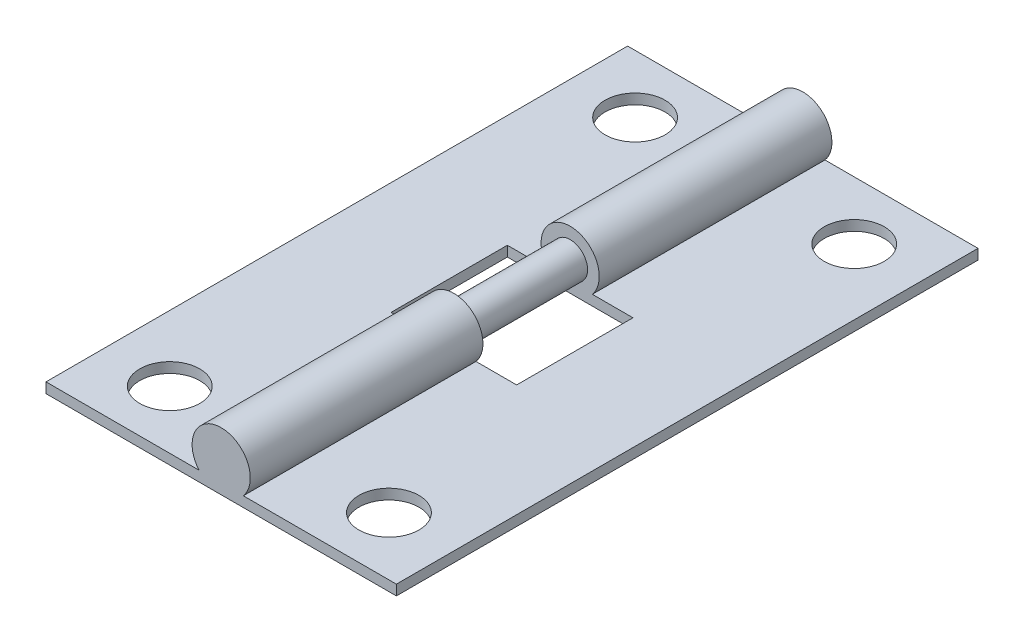
SolidWorks part; units mm, degrees
ref_plane "Front Plane" through (0, 0, 0) normal (0, 0, 1) x (1, 0, 0)
ref_plane "Top Plane" through (0, 0, 0) normal (0, 1, 0) x (1, 0, 0)
ref_plane "Right Plane" through (0, 0, 0) normal (1, 0, 0) x (0, 0, -1)
sketch "Sketch1" plane through (0, 0, 0) normal (0, 0, 1) x (1, 0, 0)
  line L0 (0, 0) -> (19.1262, 0)
  line L1 (19.1262, 0) -> (19.1262, 0.5588)
  line L2 (19.1262, 0.5588) -> (10.7722, 0.5588)
  line L3 (0, 0) -> (0, 0.5588)
  line L4 (0, 0.5588) -> (8.354, 0.5588)
  arc A0 (10.7722, 0.5588) -> (8.354, 0.5588) centre (9.5631, 1.5875) ccw
  dimension "D2" = 3.175
  dimension "D1" = 19.1262
  dimension "D3" = 0.5588
  dimension "D4" = 1.5875
  dimension "D5" = 9.5631
extrude "Boss-Extrude1" add sketch "Sketch1" along normal blind 31.75
sketch "Sketch3" plane through (0, 0, 0) normal (0, -1, 0) x (1, 0, 0)
  line L0 (3.5814, 31.75) -> (3.5814, 0) construction
  line L1 (0, 31.75) -> (19.1262, 31.75) construction
  line L2 (0, 0) -> (19.1262, 0) construction
  line L3 (15.5448, 31.75) -> (15.5448, 0) construction
  line L4 (0, 31.75) -> (0, 0) construction
  line L5 (19.1262, 31.75) -> (19.1262, 0) construction
  line L6 (0, 0) -> (19.1262, 0)
  line L7 (6.1341, 19.05) -> (12.9921, 19.05)
  line L8 (6.1341, 19.05) -> (6.1341, 12.7)
  line L9 (6.1341, 12.7) -> (12.9921, 12.7)
  line L10 (12.9921, 19.05) -> (12.9921, 12.7)
  line L11 (6.1341, 19.05) -> (12.9921, 12.7) construction
  line L12 (6.1341, 12.7) -> (12.9921, 19.05) construction
  circle A0 centre (3.5814, 28.575) radius 1.6383
  circle A1 centre (3.5814, 3.175) radius 1.6383
  circle A2 centre (15.5448, 3.175) radius 1.6383
  circle A3 centre (15.5448, 28.575) radius 1.6383
  point P26 (9.5631, 15.875)
  dimension "D3" = 3.2766
  dimension "D1" = 3.5814
  dimension "D2" = 3.5814
  dimension "D4" = 25.4
  dimension "D5" = 3.175
  dimension "D6" = 3.175
  dimension "D7" = 25.4
  dimension "D8" = 12.7
  dimension "D9" = 6.858
  dimension "D10" = 6.35
  dimension "D11" = 19.1262
  dimension "D12" = 9.5631
extrude "Cut-Extrude1" cut sketch "Sketch3" against normal through all contours L10 L7 L8 L9 | A0 | A3 | A2 | A1
sketch "Sketch4" plane through (0, 0, 12.7) normal (0, 0, 1) x (1, 0, 0)
  circle A0 centre (9.5631, 1.5875) radius 0.9525
  dimension "D1" = 1.905
extrude "Boss-Extrude2" add sketch "Sketch4" along normal up to next
equation "\"D4@Sketch1\"=.125-\"D2@Sketch1\"/2"
equation "\"D5@Sketch1\"=\"D1@Sketch1\"/2"
equation "\"D2@Sketch3\"=\"D1@Sketch3\""
equation "\"D6@Sketch3\"=\"D5@Sketch3\""
equation "\"D7@Sketch3\"=\"D4@Sketch3\""
equation "\"D8@Sketch3\"=\"D4@Sketch3\"/2"
equation "\"D12@Sketch3\"=\"D11@Sketch3\"/2"
